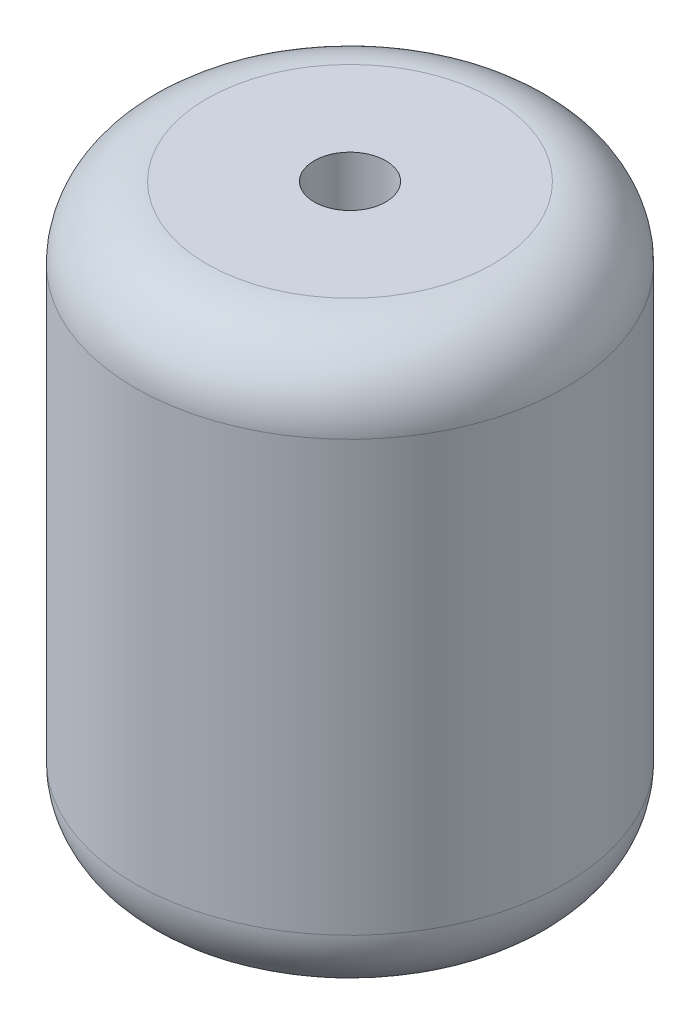
SolidWorks part; units mm, degrees
ref_plane "前视基准面" through (0, 0, 0) normal (0, 0, 1) x (1, 0, 0)
ref_plane "上视基准面" through (0, 0, 0) normal (0, 1, 0) x (1, 0, 0)
ref_plane "右视基准面" through (0, 0, 0) normal (1, 0, 0) x (0, 0, -1)
sketch "草图1" plane through (0, 0, 0) normal (0, 1, 0) x (1, 0, 0)
  circle A0 centre (0, 0) radius 3
  circle A1 centre (0, 0) radius 0.5
  dimension "D1" = 6
  dimension "D2" = 1
extrude "凸台-拉伸1" add sketch "草图1" along normal blind 8
fillet "圆角1" radius 1 2 edges at (0, 8, 3) (0, 0, 3)
